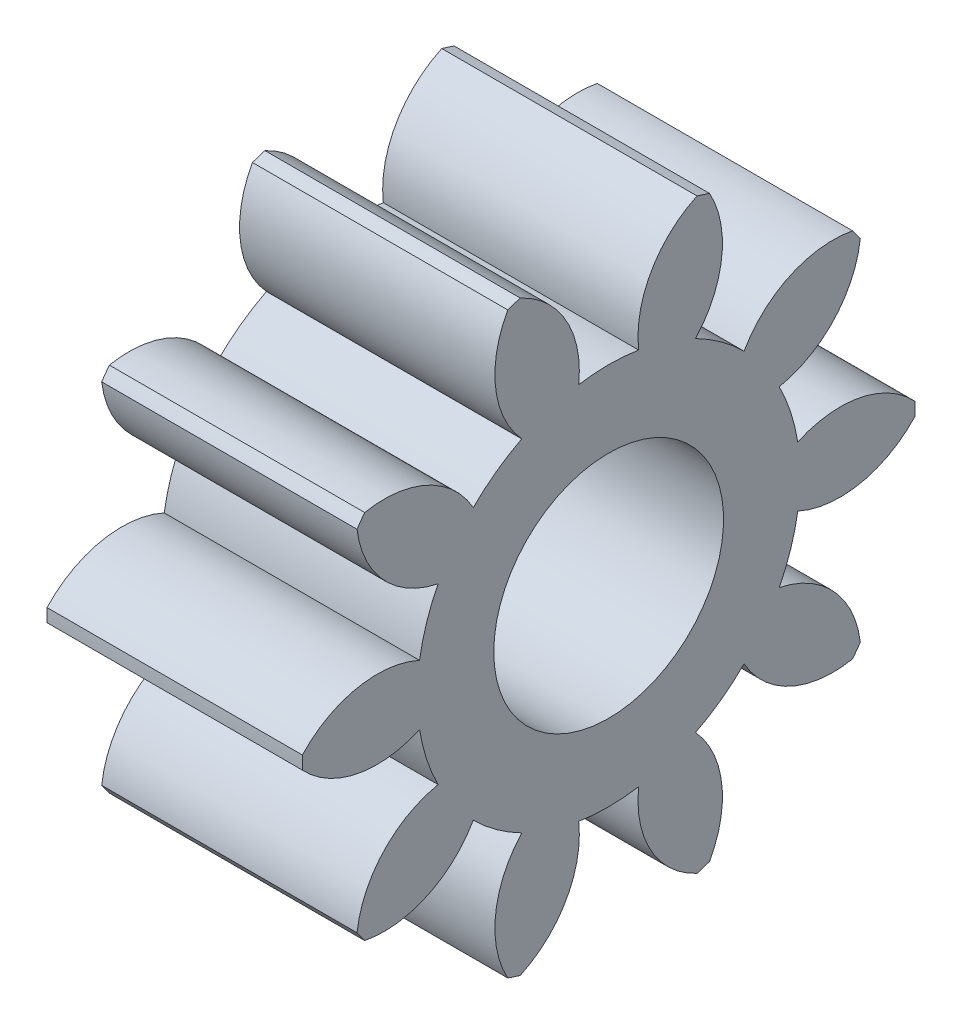
SolidWorks part; units mm, degrees
ref_plane "Plane1" through (0, 0, 0) normal (0, 0, 1) x (1, 0, 0)
ref_plane "Plane2" through (0, 0, 0) normal (0, 1, 0) x (1, 0, 0)
ref_plane "Plane3" through (0, 0, 0) normal (1, 0, 0) x (0, 0, -1)
sketch "HoldingSke" plane through (0, 0, 0) normal (0, 1, 0) x (1, 0, 0)
  line L0 (0, 0) -> (0.4924, -0.0868)
  line L1 (-15, 0) -> (100, 0) construction
  line L2 (0, 0) -> (-2.1039, 2.3779)
  line L3 (0, 0) -> (-11.863, 4.5341)
  line L4 (0, 0) -> (8.5048, 1.4996)
  line L5 (0, 0) -> (-46.8476, -17.4728)
  line L6 (0, 0) -> (-8.2896, -5.593)
  line L7 (-2.1039, 2.3779) -> (8.6586, 51.2059)
  line L8 (-76.2, 54.61) -> (-74.8, 54.61)
  line L9 (-71.009, 38.7566) -> (-53.1078, 45.2721)
  line L10 (-76.2, 71.12) -> (104.1128, 71.12)
  line L11 (0, 0) -> (-10, 0)
  line L12 (-76.2, 101.6) -> (-76.133, 101.6)
  line L13 (24.9733, 27.94) -> (52.9518, 28.4284)
  line L14 (24.9733, 27.94) -> (24.9743, 27.94)
  line L15 (24.9733, 27.94) -> (100.4006, 29.5858)
  line L16 (-63.627, -2) -> (-12.827, -2)
  circle A0 centre (0, 0) radius 4.5
  circle A1 centre (0, 0) radius 7.499
  circle A2 centre (0, 0) radius 37.5
  circle A3 centre (0, 0) radius 4.5
  dimension "MHD" = 14.998
  dimension "Hub_dia" = 75
  dimension "Bore" = 9
  dimension "MBD" = 9
  dimension "Num_teeth" = 10
  dimension "Pitch" = 0.5
  dimension "Overall_len" = 50
  dimension "Show_teeth" = 10
  dimension "Thickness" = 10
  dimension "OAL" = 50.0001
  dimension "T_dim" = 1.4
  dimension "Ap" = 20
  dimension "H" = 19.05
  dimension "Pitch_radius" = 180.3128
  dimension "Width" = 10
  dimension "Backlash" = 0.067
  dimension "Addendum_fac" = 1
  dimension "Dedendum_fac" = 1.25
  dimension "Clearance_fac" = 0.25
  dimension "Dedendum_add" = 0.001
  dimension "Module" = 2
sketch "BasProSke" plane through (0, 0, 0) normal (0, 1, 0) x (1, 0, 0)
  line L0 (-10, 0) -> (60, 0) construction
  line L1 (0, 0) -> (0, 12)
  line L2 (0, 0) -> (10, 0)
  line L3 (10, 0) -> (10, 12)
  line L4 (10, 12) -> (0, 12)
  dimension "Thickness" = 10
  dimension "Diameter" = 24
revolve "Base-Revolve" add sketch "BasProSke" angle 360 about L0
sketch "TooCutSke" plane through (0, 0, 0) normal (1, 0, 0) x (0, 0, -1)
  line L1 (0, 0) -> (0, 107) construction
  line L2 (0, 0) -> (-1.6814, 9.8576) construction
  line L3 (0, 0) -> (-6.1153, 18.8209) construction
  line L4 (-1.6814, 9.8576) -> (-3.0576, 9.4105) construction
  arc A0 (1.1737, 7.4066) -> (-1.1737, 7.4066) centre (0, 0) ccw
  arc A1 (3.4979, 11.5054) -> (-3.4979, 11.5054) centre (0, 0) ccw
  circle A2 centre (0, 0) radius 10 construction
  circle A3 centre (0, 0) radius 9.3969 construction
  arc A4 (-1.1737, 7.4066) -> (-3.4979, 11.5054) centre (-5.1477, 7.8615) ccw
  arc A5 (3.4979, 11.5054) -> (1.1737, 7.4066) centre (5.1477, 7.8615) ccw
  dimension "Root_dia" = 14.998
  dimension "Overcut_dia" = 24.0508
  dimension "Pitch_dia" = 20
  dimension "Base_dia" = 18.7939
  dimension "Flank_rad" = 4
  dimension "Half_ang" = 18
  dimension "Half_CT" = 1.4471
extrude "ToothCut" cut sketch "TooCutSke" along normal through all
fillet "Breaks" [suppressed] radius 0.04
fillet "RootFillets" [suppressed] radius 0.501
pattern_circular "TeethCuts" count 10 every 36 about axis through (-10, 0, 0) along (1, 0, 0) of "ToothCut", "RootFillets", "Breaks"
sketch "HubNeaOneSke" plane through (0, 0, 0) normal (-1, 0, 0) x (0, 0, 1)
  circle A0 centre (0, 0) radius 7.499
  dimension "Diameter" = 14.998
extrude "HubNearOne" [suppressed] add sketch "HubNeaOneSke" along normal blind 40.0001
sketch "HubNeaBotSke" plane through (0, 0, 0) normal (-1, 0, 0) x (0, 0, 1)
  circle A0 centre (0, 0) radius 7.499
  dimension "Diameter" = 14.998
extrude "HubNearBoth" [suppressed] add sketch "HubNeaBotSke" along normal blind 20
ref_plane "FarPln" through (10, 0, 0) normal (1, 0, 0) x (0, 0, -1)
sketch "HubFarSke" plane through (10, 0, 0) normal (1, 0, 0) x (0, 0, -1)
  circle A0 centre (0, 0) radius 7.499
  dimension "Diameter" = 14.998
extrude "HubFar" [suppressed] add sketch "HubFarSke" along normal blind 20
sketch "BorSke" plane through (0, 0, 0) normal (1, 0, 0) x (0, 0, -1)
  circle A0 centre (0, 0) radius 4.5
  dimension "Diameter" = 9
extrude "Bore" cut sketch "BorSke" along normal mid plane 100.0001
sketch "KeySke" plane through (0, 0, 0) normal (1, 0, 0) x (0, 0, -1)
  line L0 (-1.5, 0) -> (-1.5, 5.9)
  line L1 (-1.5, 5.9) -> (1.5, 5.9)
  line L2 (1.5, 5.9) -> (1.5, 0)
  line L3 (0, 0) -> (0, 34) construction
  line L4 (-1.5, 0) -> (1.5, 0)
  dimension "Offset" = 5.9
  dimension "Width" = 3
extrude "Keyway" [suppressed] cut sketch "KeySke" along normal mid plane 100.0001
pattern_circular "Keyway2" [suppressed] count 2 every 90 about axis through (-10, 0, 0) along (1, 0, 0)
equation "' \"Module@HoldingSke\" = 6.35"
equation "' \"Num_teeth@HoldingSke\" = 12"
equation "' \"Ap@HoldingSke\" =  20"
equation "' \"Ap@HoldingSke\" = 20"
equation "' \"Width@HoldingSke\" = 0.5 * 25.4"
equation "' \"Hub_dia@HoldingSke\"= 1 * 25.4"
equation "' \"Hub_dia@HoldingSke\" = 1 * 25.4"
equation "' \"Overall_len@HoldingSke\" = 1.0 * 25.4"
equation "' \"Bore@HoldingSke\" = 0.75 * 25.4"
equation "' \"T_dim@HoldingSke\" = 0.1 * 25.4"
equation "' \"Width@KeySke\" = 0.25 * 25.4"
equation "' \"Show_teeth@HoldingSke\" = 13"
equation "' \"Backlash@HoldingSke\" = 0.009 * 25.4"
equation "' \"Addendum_fac@HoldingSke\" = 1.0"
equation "' \"Dedendum_fac@HoldingSke\" = 1.25"
equation "' \"Dedendum_add@HoldingSke\" = 0.00005 * 25.4"
equation "' \"Clearance_fac@HoldingSke\" = 0.25"
equation "\"Pitch@HoldingSke\" = 1 / \"Module@HoldingSke\""
equation "\"Overcut_dia@TooCutSke\" = (\"Num_teeth@HoldingSke\" + 2 * \"Addendum_fac@HoldingSke\") / \"Pitch@HoldingSke\" + 0.002 * 25.4"
equation "\"Pitch_dia@TooCutSke\" = \"Num_teeth@HoldingSke\" / \"Pitch@HoldingSke\""
equation "\"Base_dia@TooCutSke\" = \"Num_teeth@HoldingSke\" / \"Pitch@HoldingSke\" * cos((\"Ap@HoldingSke\"  * 3.14159265 / 180))"
equation "\"Root_dia@TooCutSke\" = (\"Num_teeth@HoldingSke\" + 2) / \"Pitch@HoldingSke\" - 2 * (\"Addendum_fac@HoldingSke\" + \"Dedendum_fac@HoldingSke\") / \"Pitch@HoldingSke\" - \"Dedendum_add@HoldingSke\" * 2"
equation "\"Half_ang@TooCutSke\" = 180 / \"Num_teeth@HoldingSke\""
equation "\"Half_CT@TooCutSke\" = \"Num_teeth@HoldingSke\" / \"Pitch@HoldingSke\" * sin((3.14159265 / 2 / \"Num_teeth@HoldingSke\")) / 2 - 7 * \"Backlash@HoldingSke\" / 4"
equation "\"Flank_rad@TooCutSke\" = \"Num_teeth@HoldingSke\" / \"Pitch@HoldingSke\" / 5"
equation "\"Radius@RootFillets\" = \"Clearance_fac@HoldingSke\" / \"Pitch@HoldingSke\" + \"Dedendum_add@HoldingSke\""
equation "\"Break_rad@Breaks\" = 0.02 / \"Pitch@HoldingSke\""
equation "\"Thickness@HoldingSke\" = \"Width@HoldingSke\""
equation "\"OAL@HoldingSke\" = \"Thickness@HoldingSke\""
equation "\"MHD@HoldingSke\" = (\"Num_teeth@HoldingSke\" + 2) / \"Pitch@HoldingSke\" - 2 * (\"Addendum_fac@HoldingSke\" + \"Dedendum_fac@HoldingSke\")  / \"Pitch@HoldingSke\" - \"Dedendum_add@HoldingSke\" * 2"
equation "\"MBD@HoldingSke\" = (\"Num_teeth@HoldingSke\" + 2) / \"Pitch@HoldingSke\" - 2 * (\"Addendum_fac@HoldingSke\" + \"Dedendum_fac@HoldingSke\")  / \"Pitch@HoldingSke\" - \"Dedendum_add@HoldingSke\" * 2 - 0.002 * 25.4"
equation "\"MHD@HoldingSke\" = ((sgn( \"MHD@HoldingSke\" - \"Hub_dia@HoldingSke\" )-1)*( \"MHD@HoldingSke\" - \"Hub_dia@HoldingSke\" ))/-2+ \"Hub_dia@HoldingSke\""
equation "\"MBD@HoldingSke\" = ((sgn( \"MBD@HoldingSke\" - \"Bore@HoldingSke\" )-1)*( \"MBD@HoldingSke\" - \"Bore@HoldingSke\" ))/-2+ \"Bore@HoldingSke\""
equation "\"OAL@HoldingSke\" = ((sgn( \"OAL@HoldingSke\" - \"Overall_len@HoldingSke\" )+1)*( \"OAL@HoldingSke\" - \"Overall_len@HoldingSke\" ))/2 + \"Overall_len@HoldingSke\" + 0.000002 * 25.4"
equation "\"Num_teeth@TeethCuts\" = int( \"Show_teeth@HoldingSke\" ) + 1"
equation "\"Num_teeth@TeethCuts\" = ((sgn( \"Num_teeth@TeethCuts\" - \"Num_teeth@HoldingSke\" )-1)*( \"Num_teeth@TeethCuts\" - \"Num_teeth@HoldingSke\" ))/-2+ \"Num_teeth@HoldingSke\""
equation "\"Num_teeth@TeethCuts\" = ((sgn( \"Num_teeth@TeethCuts\" - 2.0)+1)*( \"Num_teeth@TeethCuts\" - 2.0))/2 +2.0"
equation "\"Angle@TeethCuts\" = 360.0 / \"Num_teeth@HoldingSke\""
equation "\"Diameter@BasProSke\" = (\"Num_teeth@HoldingSke\" + 2 * \"Addendum_fac@HoldingSke\") / \"Pitch@HoldingSke\""
equation "\"Thickness@BasProSke\"  = \"Thickness@HoldingSke\""
equation "' \"Fillet_rad@BasProSke\" =  \"Thickness@HoldingSke\" * 0.05"
equation "' \"Fillet_rad@BasProSke\" = \"Thickness@HoldingSke\" * 0.05"
equation "\"MHD@HoldingSke\" = ((sgn( \"MHD@HoldingSke\" - \"Root_dia@TooCutSke\" )-1)*( \"MHD@HoldingSke\" - \"Root_dia@TooCutSke\" ))/-2+ \"Root_dia@TooCutSke\""
equation "\"Diameter@HubNeaOneSke\" = \"MHD@HoldingSke\""
equation "\"Length@HubNearOne\" = \"OAL@HoldingSke\" - \"Thickness@BasProSke\""
equation "\"Diameter@HubNeaBotSke\" = \"MHD@HoldingSke\""
equation "\"Length@HubNearBoth\" = ( \"OAL@HoldingSke\" - \"Thickness@BasProSke\" ) / 2.0"
equation "\"Thickness@FarPln\" = \"Thickness@BasProSke\""
equation "\"Diameter@HubFarSke\" = \"MHD@HoldingSke\""
equation "\"Length@HubFar\" = ( \"OAL@HoldingSke\" - \"Thickness@BasProSke\" ) / 2.0"
equation "\"Diameter@BorSke\" = \"MBD@HoldingSke\""
equation "\"D1@Bore\" = \"OAL@HoldingSke\" * 2.0"
equation "\"D1@Keyway\" = \"OAL@HoldingSke\" * 2.0"
equation "\"Offset@KeySke\" = \"T_dim@HoldingSke\" + \"MBD@HoldingSke\" / 2.0"
